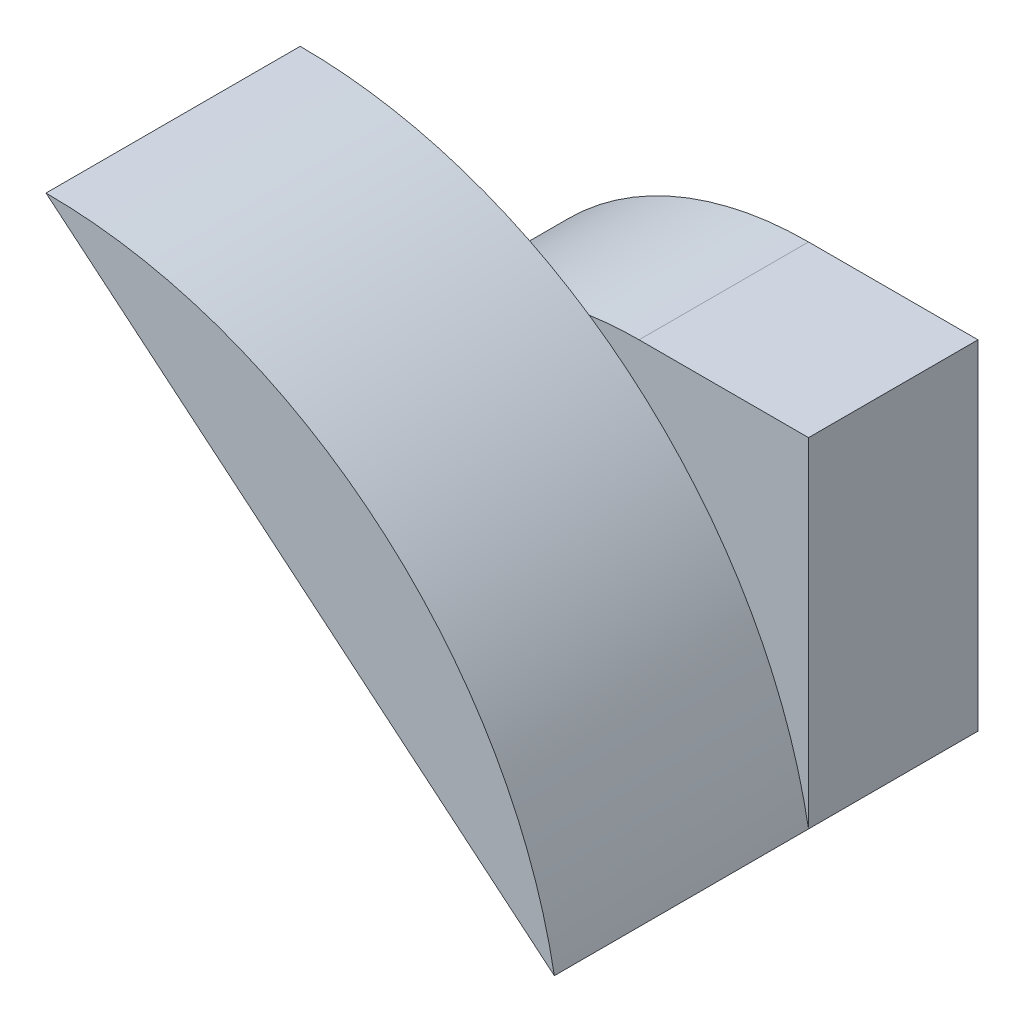
SolidWorks part; units mm, degrees
ref_plane "Front Plane" through (0, 0, 0) normal (0, 0, 1) x (1, 0, 0)
ref_plane "Top Plane" through (0, 0, 0) normal (0, 1, 0) x (1, 0, 0)
ref_plane "Right Plane" through (0, 0, 0) normal (1, 0, 0) x (0, 0, -1)
sketch "Sketch1" plane through (0, 0, 0) normal (0, 0, 1) x (1, 0, 0)
  line L0 (-30, 0) -> (0, 0)
  line L1 (0, 0) -> (0, 20)
  line L2 (0, 20) -> (-10, 20)
  arc A0 (-10, 20) -> (-30, 0) centre (-10, 0) ccw
  dimension "D1" = 30
  dimension "D2" = 20
  dimension "D3" = 10
extrude "Boss-Extrude1" add sketch "Sketch1" along normal blind 10
sketch "Sketch2" plane through (0, 0, 10) normal (0, 0, 1) x (1, 0, 0)
  line L0 (0, 0) -> (-30, 25)
  arc A0 (-30, 25) -> (0, 0) centre (-30, -5.5) cw
  dimension "D1" = 25
extrude "Boss-Extrude2" add sketch "Sketch2" along normal blind 15
